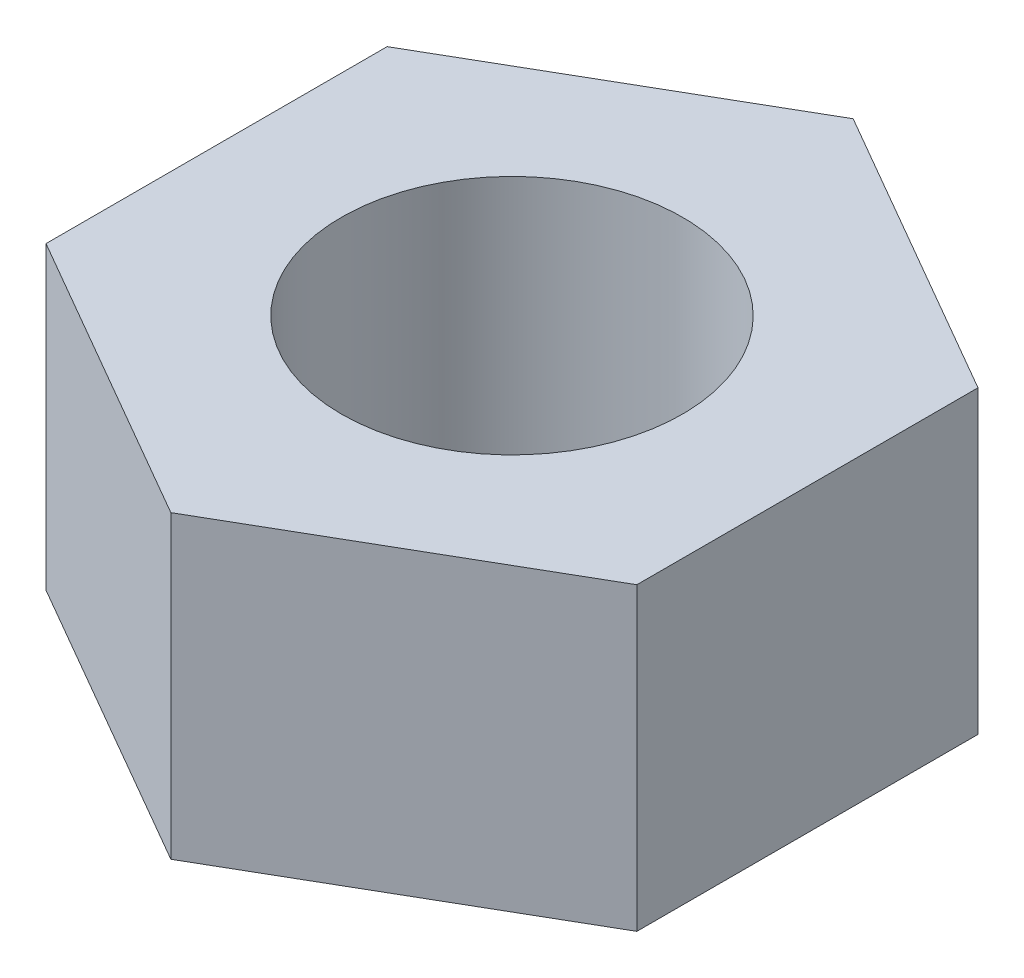
SolidWorks part; units mm, degrees
ref_plane "Front Plane" through (0, 0, 0) normal (0, 0, 1) x (1, 0, 0)
ref_plane "Top Plane" through (0, 0, 0) normal (0, 1, 0) x (1, 0, 0)
ref_plane "Right Plane" through (0, 0, 0) normal (1, 0, 0) x (0, 0, -1)
sketch "Sketch1" plane through (0, 0, 0) normal (0, 1, 0) x (1, 0, 0)
  line L1 (0, 6.3498) -> (-5.4991, 3.1749)
  line L2 (-5.4991, 3.1749) -> (-5.4991, -3.1749)
  line L3 (-5.4991, -3.1749) -> (0, -6.3498)
  line L4 (0, -6.3498) -> (5.4991, -3.1749)
  line L5 (5.4991, -3.1749) -> (5.4991, 3.1749)
  line L6 (5.4991, 3.1749) -> (0, 6.3498)
  circle A0 centre (0, 0) radius 5.4991 construction
  circle A1 centre (0, 0) radius 3.175
extrude "Boss-Extrude1" add sketch "Sketch1" along normal blind 5.588
